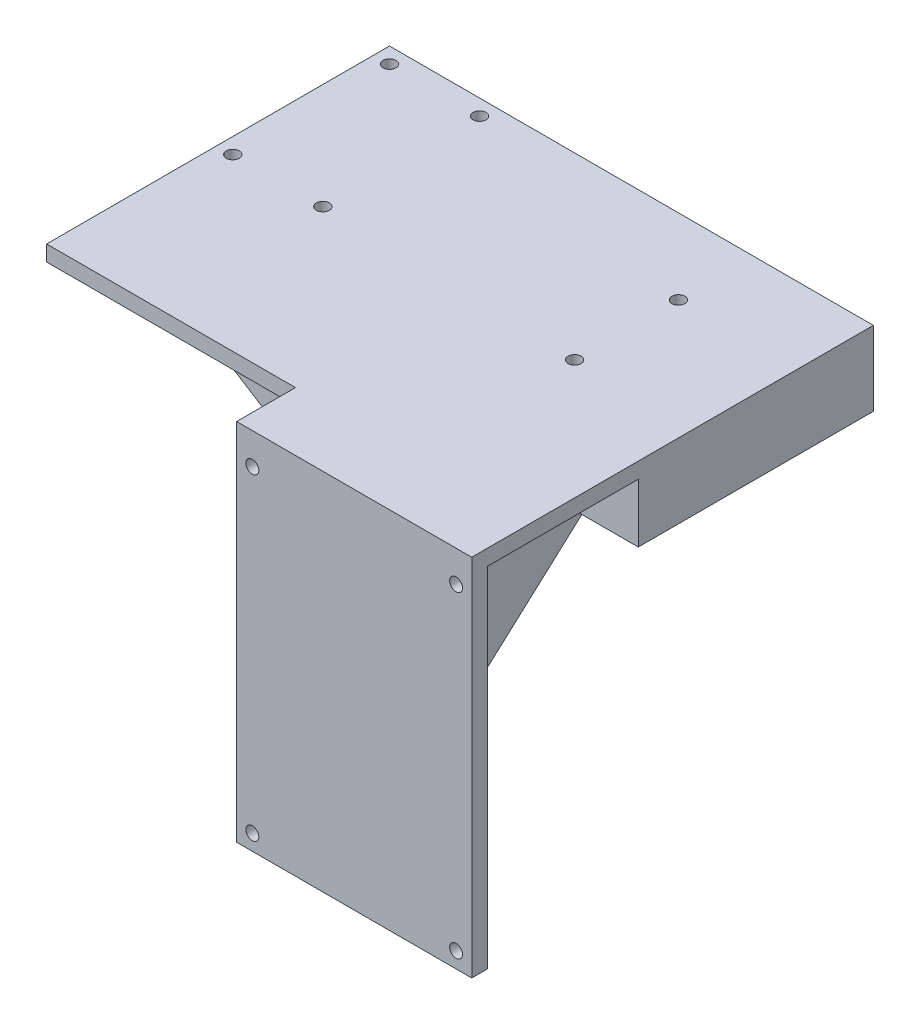
SolidWorks part; units mm, degrees
ref_plane "Front Plane" through (0, 0, 0) normal (0, 0, 1) x (1, 0, 0)
ref_plane "Top Plane" through (0, 0, 0) normal (0, 1, 0) x (1, 0, 0)
ref_plane "Right Plane" through (0, 0, 0) normal (1, 0, 0) x (0, 0, -1)
sketch "Sketch1" plane through (0, 0, 0) normal (0, 0, 1) x (1, 0, 0)
  line L1 (0, 0) -> (60, 0)
  line L2 (0, 0) -> (0, -93)
  line L3 (0, -93) -> (60, -93)
  line L4 (60, 0) -> (60, -93)
  dimension "D1" = 93
  dimension "D2" = 60
extrude "Boss-Extrude1" add sketch "Sketch1" against normal blind 4
sketch "Sketch2" plane through (0, 0, 0) normal (0, 0, 1) x (1, 0, 0)
  line L0 (0, 0) -> (0, -93) construction
  line L1 (60, 0) -> (0, 0)
  line L2 (60, 0) -> (60, -4)
  line L3 (60, -4) -> (0, -4)
  line L4 (0, 0) -> (0, -4)
  dimension "D1" = 4
sketch "Sketch3" plane through (0, 0, 0) normal (0, 0, 1) x (1, 0, 0)
  line L0 (60, -4) -> (0, -4) construction
  line L1 (0, 0) -> (0, -93) construction
  line L2 (60, -93) -> (60, 0) construction
  line L3 (0, -93) -> (60, -93) construction
  circle A0 centre (4, -8) radius 1.65
  circle A1 centre (56, -8) radius 1.65
  circle A2 centre (4, -89) radius 1.65
  circle A3 centre (56, -89) radius 1.65
  dimension "D1" = 3.3
  dimension "D4" = 3.3
  dimension "D9" = 3.3
  dimension "D12" = 3.3
  dimension "D2" = 4
  dimension "D3" = 4
  dimension "D5" = 4
  dimension "D6" = 4
  dimension "D7" = 4
  dimension "D8" = 4
  dimension "D10" = 4
  dimension "D11" = 4
extrude "Cut-Extrude1" cut sketch "Sketch3" against normal blind 4
sketch "Sketch5" plane through (0, 0, -4) normal (0, 0, -1) x (-1, 0, 0)
  line L0 (0, 0) -> (0, -93) construction
  line L1 (-60, 0) -> (0, 0)
  line L2 (-60, 0) -> (-60, -4)
  line L3 (-60, -4) -> (0, -4)
  line L4 (0, 0) -> (0, -4)
  dimension "D1" = 4
extrude "Boss-Extrude2" add sketch "Sketch5" along normal blind 11
sketch "Sketch6" plane through (0, 0, -15) normal (0, 0, -1) x (-1, 0, 0)
  line L1 (-60, -4) -> (63.5, -4)
  line L2 (-60, -4) -> (-60, 0)
  line L3 (-60, 0) -> (63.5, 0)
  line L4 (63.5, -4) -> (63.5, 0)
  dimension "D1" = 123.5
  dimension "D2" = 4
extrude "Boss-Extrude3" add sketch "Sketch6" along normal blind 87.5
sketch "Sketch7" plane through (0, 0, 0) normal (0, 1, 0) x (1, 0, 0)
  line L0 (-63.5, 102.5) -> (60, 102.5) construction
  line L1 (-63.5, 102.5) -> (-63.5, 15) construction
  circle A0 centre (-59.5, 98.5) radius 1.65
  circle A1 centre (-36.5, 98.5) radius 1.65
  circle A2 centre (-59.5, 58.5) radius 1.65
  circle A3 centre (-36.5, 58.5) radius 1.65
  dimension "D5" = 3.3
  dimension "D6" = 3.3
  dimension "D9" = 3.3
  dimension "D11" = 44
  dimension "D12" = 3.3
  dimension "D1" = 4
  dimension "D2" = 4
  dimension "D3" = 4
  dimension "D4" = 23
  dimension "D7" = 4
  dimension "D8" = 40
  dimension "D10" = 23
extrude "Cut-Extrude2" cut sketch "Sketch7" against normal blind 87.5
sketch "Sketch8" plane through (0, 0, 0) normal (0, 1, 0) x (1, 0, 0)
  line L1 (-36.5, 58.5) -> (-18, 58.5)
  line L2 (-36.5, 58.5) -> (-36.5, 70)
  line L3 (-36.5, 70) -> (-18, 70)
  line L4 (-18, 58.5) -> (-18, 70)
  dimension "D1" = 18.5
  dimension "D2" = 11.5
sketch "Sketch9" plane through (0, 0, 0) normal (0, 1, 0) x (1, 0, 0)
  line L1 (-18, 70) -> (29.5, 70)
  line L2 (-18, 70) -> (-18, 83.25)
  line L3 (-18, 83.25) -> (29.5, 83.25)
  line L4 (29.5, 70) -> (29.5, 83.25)
  line L5 (-18, 70) -> (29.5, 70)
  line L6 (-18, 70) -> (-18, 56.75)
  line L7 (-18, 56.75) -> (29.5, 56.75)
  line L8 (29.5, 70) -> (29.5, 56.75)
  dimension "D1" = 13.25
  dimension "D2" = 47.5
  dimension "D3" = 13.25
sketch "Sketch10" plane through (0, 0, 0) normal (0, 1, 0) x (1, 0, 0)
  circle A0 centre (29.5, 83.25) radius 1.65
  circle A1 centre (29.5, 56.75) radius 1.65
  dimension "D1" = 3.3
  dimension "D2" = 3.3
extrude "Cut-Extrude3" cut sketch "Sketch10" against normal blind 10
sketch "Sketch11" plane through (0, 0, 0) normal (1, 0, 0) x (0, 0, -1)
  line L0 (15, -4) -> (4, -4) construction
  line L1 (4, -93) -> (102.5, -93)
  line L2 (4, -93) -> (4, -4)
  line L3 (4, -4) -> (102.5, -4)
  line L4 (102.5, -93) -> (102.5, -4)
  line L5 (4, -4) -> (4, -93) construction
  dimension "D1" = 0
  dimension "D2" = 89
  dimension "D3" = 98.5
  dimension "D4" = 0
extrude "Boss-Extrude4" add sketch "Sketch11" along normal blind 25
sketch "Sketch13" plane through (0, 0, 0) normal (-1, 0, 0) x (0, 0, 1)
  line L0 (-102.5, -93) -> (0, -93) construction
  line L1 (-102.5, -4) -> (-4, -4)
  line L2 (-102.5, -4) -> (-102.5, -93)
  line L3 (-102.5, -93) -> (-4, -93)
  line L4 (-4, -4) -> (-4, -93)
  line L5 (0, 0) -> (0, -93) construction
  dimension "D1" = 4
extrude "Cut-Extrude5" cut sketch "Sketch13" against normal blind 8
sketch "Sketch14" plane through (8, 0, 0) normal (-1, 0, 0) x (0, 0, 1)
  line L0 (-102.5, -4) -> (-102.5, -93)
  line L1 (-102.5, -93) -> (-4, -93)
  line L2 (-102.5, -4) -> (-4, -93)
extrude "Cut-Extrude7" cut sketch "Sketch14" against normal blind 20
sketch "Sketch15" plane through (0, -4, 0) normal (0, -1, 0) x (1, 0, 0)
  line L0 (-63.5, -102.5) -> (-63.5, -15) construction
  line L1 (-63.5, -50.5) -> (8, -50.5)
  line L2 (-63.5, -50.5) -> (-63.5, -33.5)
  line L3 (-63.5, -33.5) -> (8, -33.5)
  line L4 (8, -50.5) -> (8, -33.5)
  line L5 (8, -4) -> (8, -102.5) construction
  line L6 (0, -15) -> (-63.5, -15) construction
  circle A0 centre (-59.5, -58.5) radius 1.65 construction
  dimension "D1" = 8
  dimension "D2" = 18.5
  dimension "D3" = 17
extrude "Boss-Extrude6" add sketch "Sketch15" along normal blind 45
sketch "Sketch16" plane through (0, 0, -50.5) normal (0, 0, -1) x (-1, 0, 0)
  line L0 (63.5, -4) -> (-8, -49)
  line L1 (63.5, -49) -> (63.5, -4)
  line L2 (-8, -49) -> (63.5, -49)
extrude "Cut-Extrude9" cut sketch "Sketch16" against normal blind 45
sketch "Sketch17" plane through (0, -4, 0) normal (0, -1, 0) x (1, 0, 0)
  line L1 (60, -102.5) -> (35, -102.5)
  line L2 (60, -102.5) -> (60, -42.5)
  line L3 (60, -42.5) -> (35, -42.5)
  line L4 (35, -102.5) -> (35, -42.5)
  dimension "D1" = 25
  dimension "D2" = 60
extrude "Boss-Extrude7" add sketch "Sketch17" along normal blind 15
